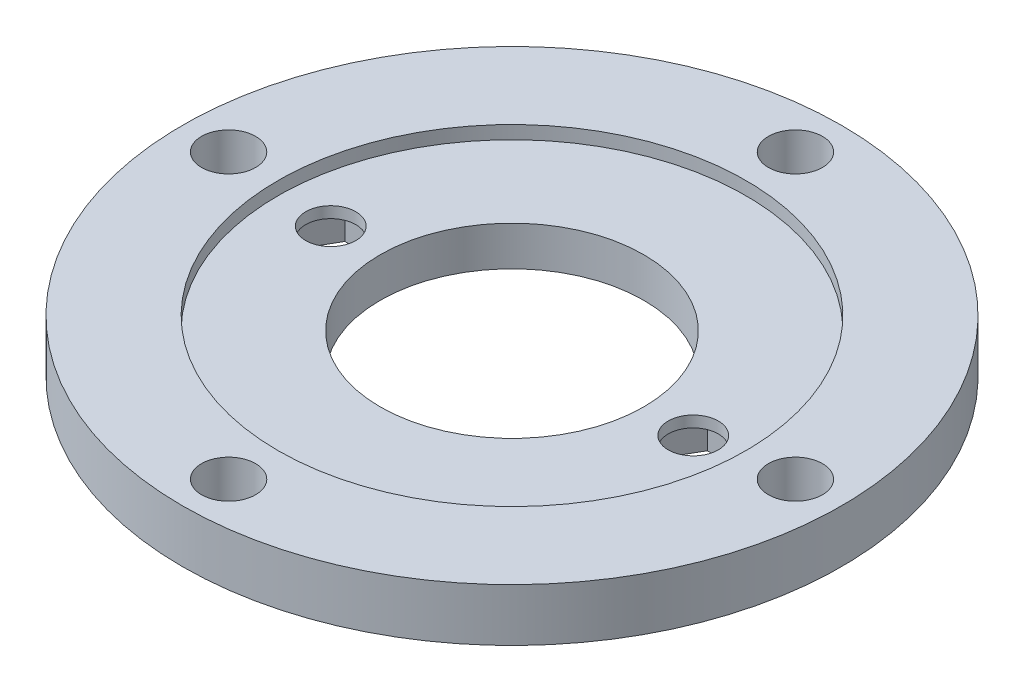
SolidWorks part; units mm, degrees
ref_plane "Front Plane" through (0, 0, 0) normal (0, 0, 1) x (1, 0, 0)
ref_plane "Top Plane" through (0, 0, 0) normal (0, 1, 0) x (1, 0, 0)
ref_plane "Right Plane" through (0, 0, 0) normal (1, 0, 0) x (0, 0, -1)
sketch "Sketch1" plane through (0, 0, 0) normal (0, 1, 0) x (1, 0, 0)
  circle A0 centre (0, 0) radius 50
  circle A1 centre (0, 0) radius 35.5
  dimension "D1" = 100
  dimension "D2" = 71
extrude "Boss-Extrude1" add sketch "Sketch1" along normal blind 8
sketch "Sketch2" plane through (0, 8, 0) normal (0, 1, 0) x (1, 0, 0)
  circle A0 centre (0, -43) radius 4.1
  circle A1 centre (-43, 0) radius 4.1
  circle A2 centre (0, 43) radius 4.1
  circle A3 centre (43, 0) radius 4.1
  circle A4 centre (0, 0) radius 43 construction
  dimension "D1" = 86
  dimension "D2" = 8.2
  dimension "D3" = 8.2
  dimension "D4" = 8.2
  dimension "D5" = 8.2
extrude "Cut-Extrude1" cut sketch "Sketch2" against normal through all both and the other way through all
sketch "Sketch3" plane through (0, 0, 0) normal (0, 1, 0) x (1, 0, 0)
  circle A0 centre (0, 0) radius 35.5
  circle A1 centre (0, 0) radius 20
  dimension "D1" = 71
  dimension "D2" = 40
extrude "Boss-Extrude2" add sketch "Sketch3" along normal blind 6
sketch "Sketch4" plane through (0, 6, 0) normal (0, 1, 0) x (1, 0, 0)
  line L1 (-21.6688, 0) -> (-24.5844, 5.05)
  line L2 (-24.5844, 5.05) -> (-30.4156, 5.05)
  line L3 (-30.4156, 5.05) -> (-33.3312, 0)
  line L4 (-33.3312, 0) -> (-30.4156, -5.05)
  line L5 (-30.4156, -5.05) -> (-24.5844, -5.05)
  line L6 (-24.5844, -5.05) -> (-21.6688, 0)
  line L7 (33.3312, 0) -> (30.4156, 5.05)
  line L8 (30.4156, 5.05) -> (24.5844, 5.05)
  line L9 (24.5844, 5.05) -> (21.6688, 0)
  line L10 (21.6688, 0) -> (24.5844, -5.05)
  line L11 (24.5844, -5.05) -> (30.4156, -5.05)
  line L12 (30.4156, -5.05) -> (33.3312, 0)
  circle A0 centre (0, 0) radius 27.5 construction
  circle A1 centre (-27.5, 0) radius 5.05 construction
  circle A2 centre (27.5, 0) radius 5.05 construction
  dimension "D1" = 55
  dimension "D2" = 10.1
  dimension "D3" = 10.1
extrude "Cut-Extrude2" cut sketch "Sketch4" along normal blind 4.3 from surface at -6 starting at face at (-43, 0, 4.1)
sketch "Sketch5" plane through (0, 6, -6) normal (0, -1, 0) x (1, 0, 0)
  circle A0 centre (0, 6) radius 27.5 construction
  circle A1 centre (-27.5, 6) radius 3.8
  circle A2 centre (27.5, 6) radius 3.8
  circle A3 centre (0, 6) radius 20 construction
  dimension "D1" = 55
  dimension "D2" = 7.6
  dimension "D3" = 7.6
extrude "Cut-Extrude3" cut sketch "Sketch5" against normal through all both and the other way through all
